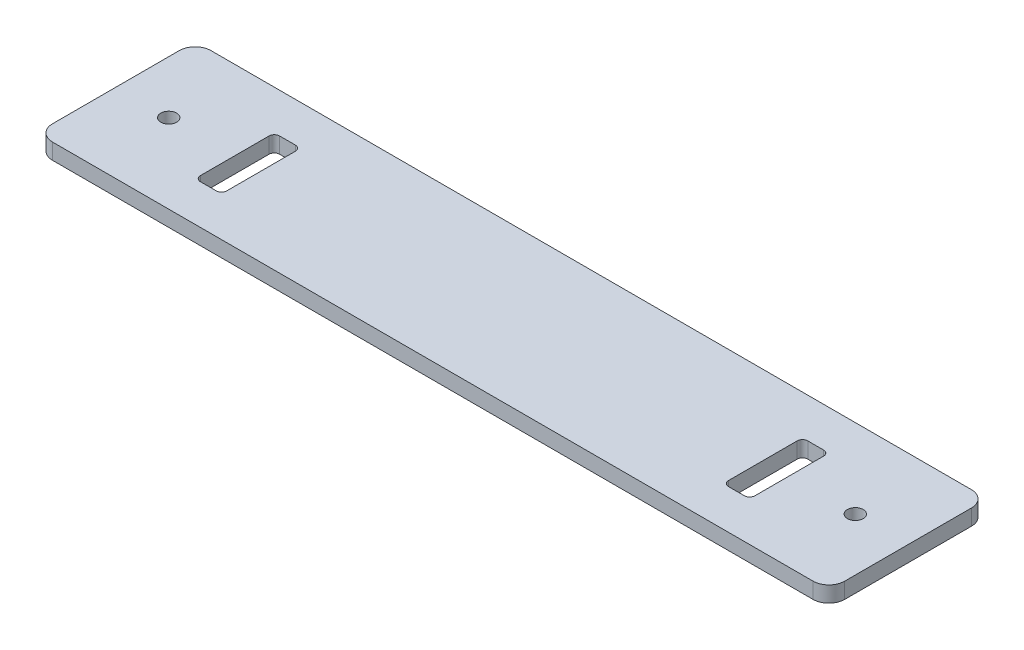
SolidWorks part; units mm, degrees
ref_plane "Front Plane" through (0, 0, 0) normal (0, 0, 1) x (1, 0, 0)
ref_plane "Top Plane" through (0, 0, 0) normal (0, 1, 0) x (1, 0, 0)
ref_plane "Right Plane" through (0, 0, 0) normal (1, 0, 0) x (0, 0, -1)
sketch "Sketch1" plane through (0, 0, 0) normal (0, 1, 0) x (1, 0, 0)
  line L0 (-75, 0) -> (75, 0) construction
  line L1 (72, 15) -> (-72, 15)
  line L2 (75, 12) -> (75, -12)
  line L3 (72, -15) -> (-72, -15)
  line L4 (-75, 12) -> (-75, -12)
  line L5 (75, 15) -> (-75, -15) construction
  line L6 (75, -15) -> (-75, 15) construction
  line L7 (0, 0) -> (0, -15) construction
  line L8 (-52.5, 7.5) -> (-47.5, -7.5) construction
  line L9 (51.5, -7.5) -> (48.5, -7.5)
  line L10 (52.5, -6.5) -> (52.5, 6.5)
  line L11 (51.5, 7.5) -> (48.5, 7.5)
  line L12 (47.5, -6.5) -> (47.5, 6.5)
  line L13 (52.5, -7.5) -> (47.5, 7.5) construction
  line L14 (52.5, 7.5) -> (47.5, -7.5) construction
  line L15 (-52.5, -7.5) -> (-47.5, 7.5) construction
  line L16 (-47.5, -6.5) -> (-47.5, 6.5)
  line L17 (-51.5, 7.5) -> (-48.5, 7.5)
  line L18 (-52.5, -6.5) -> (-52.5, 6.5)
  line L19 (-51.5, -7.5) -> (-48.5, -7.5)
  arc A0 (-72, -15) -> (-75, -12) centre (-72, -12) cw
  arc A1 (-72, 15) -> (-75, 12) centre (-72, 12) ccw
  arc A2 (75, -12) -> (72, -15) centre (72, -12) cw
  arc A3 (72, 15) -> (75, 12) centre (72, 12) cw
  circle A4 centre (65, 0) radius 1.5
  circle A5 centre (-65, 0) radius 1.5
  arc A6 (48.5, -7.5) -> (47.5, -6.5) centre (48.5, -6.5) cw
  arc A7 (51.5, -7.5) -> (52.5, -6.5) centre (51.5, -6.5) ccw
  arc A8 (48.5, 7.5) -> (47.5, 6.5) centre (48.5, 6.5) ccw
  arc A9 (52.5, 6.5) -> (51.5, 7.5) centre (51.5, 6.5) ccw
  arc A10 (-52.5, 6.5) -> (-51.5, 7.5) centre (-51.5, 6.5) cw
  arc A11 (-48.5, 7.5) -> (-47.5, 6.5) centre (-48.5, 6.5) cw
  arc A12 (-51.5, -7.5) -> (-52.5, -6.5) centre (-51.5, -6.5) cw
  arc A13 (-48.5, -7.5) -> (-47.5, -6.5) centre (-48.5, -6.5) ccw
  point P0 (0, 0)
  point P26 (50, 0)
  point P59 (-50, 0)
  dimension "D3" = 3
  dimension "D4" = 3
  dimension "D9" = 1
  dimension "D1" = 30
  dimension "D2" = 150
  dimension "D5" = 10
  dimension "D6" = 5
  dimension "D7" = 15
  dimension "D8" = 25
extrude "Boss-Extrude1" add sketch "Sketch1" along normal blind 3
